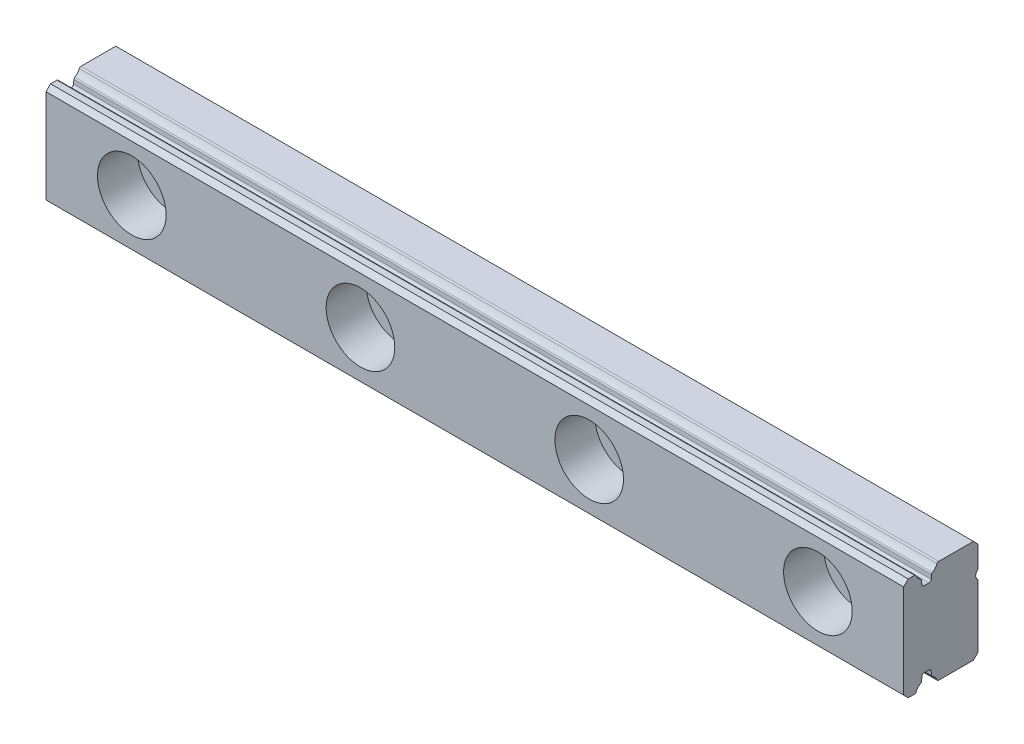
SolidWorks part; units mm, degrees
ref_plane "Front" through (0, 0, 0) normal (0, 0, 1) x (1, 0, 0)
ref_plane "Top" through (0, 0, 0) normal (0, 1, 0) x (1, 0, 0)
ref_plane "Right" through (0, 0, 0) normal (1, 0, 0) x (0, 0, -1)
ref_plane "Plane1" through (67.5, 0, 0) normal (1, 0, 0) x (0, 0, -1)
sketch "Sketch1" plane through (67.5, 0, 0) normal (1, 0, 0) x (0, 0, -1)
  line L0 (-3.4417, -4.5) -> (-0.4, -4.5)
  line L1 (-0.4, -4.5) -> (0, -4.1)
  line L2 (0, -4.1) -> (0, 1.4)
  line L3 (0, 2.2) -> (0, 4.1)
  line L4 (0, 4.1) -> (-0.4, 4.5)
  line L5 (-0.4, 4.5) -> (-3.4417, 4.5)
  line L6 (-4.0635, 3.8235) -> (-4.0934, 3.4826)
  line L7 (-4.2926, 3.3) -> (-4.7074, 3.3)
  line L8 (-4.9066, 3.4826) -> (-4.9365, 3.8235)
  line L9 (-5.5583, 4.5) -> (-6.1, 4.5)
  line L10 (-6.1, 4.5) -> (-6.5, 4.1)
  line L11 (-6.5, 4.1) -> (-6.5, -4.1)
  line L12 (-6.5, -4.1) -> (-6.1, -4.5)
  line L13 (-6.1, -4.5) -> (-5.5583, -4.5)
  line L14 (-4.9365, -3.8235) -> (-4.9066, -3.4826)
  line L15 (-4.7074, -3.3) -> (-4.2926, -3.3)
  line L16 (-4.0934, -3.4826) -> (-4.0635, -3.8235)
  arc A0 (0, 1.4) -> (0, 2.2) centre (0.3, 1.8) cw
  arc A1 (-3.4417, 4.5) -> (-3.5797, 4.4087) centre (-3.4417, 4.35) ccw
  arc A2 (-3.5797, 4.4087) -> (-3.9905, 3.9395) centre (-4.5, 4.8) cw
  arc A3 (-3.9905, 3.9395) -> (-4.0635, 3.8235) centre (-3.9141, 3.8104) ccw
  arc A4 (-4.0934, 3.4826) -> (-4.2926, 3.3) centre (-4.2926, 3.5) cw
  arc A5 (-4.7074, 3.3) -> (-4.9066, 3.4826) centre (-4.7074, 3.5) cw
  arc A6 (-4.9365, 3.8235) -> (-5.0095, 3.9395) centre (-5.0859, 3.8104) ccw
  arc A7 (-5.0095, 3.9395) -> (-5.4203, 4.4087) centre (-4.5, 4.8) cw
  arc A8 (-5.4203, 4.4087) -> (-5.5583, 4.5) centre (-5.5583, 4.35) ccw
  arc A9 (-5.5583, -4.5) -> (-5.4203, -4.4087) centre (-5.5583, -4.35) ccw
  arc A10 (-5.4203, -4.4087) -> (-5.0095, -3.9395) centre (-4.5, -4.8) cw
  arc A11 (-5.0095, -3.9395) -> (-4.9365, -3.8235) centre (-5.0859, -3.8104) ccw
  arc A12 (-4.9066, -3.4826) -> (-4.7074, -3.3) centre (-4.7074, -3.5) cw
  arc A13 (-4.2926, -3.3) -> (-4.0934, -3.4826) centre (-4.2926, -3.5) cw
  arc A14 (-4.0635, -3.8235) -> (-3.9905, -3.9395) centre (-3.9141, -3.8104) ccw
  arc A15 (-3.9905, -3.9395) -> (-3.5797, -4.4087) centre (-4.5, -4.8) cw
  arc A16 (-3.5797, -4.4087) -> (-3.4417, -4.5) centre (-3.4417, -4.35) ccw
extrude "Boss-Extrude1" add sketch "Sketch1" against normal blind 75
hole_wizard "CBORE for M3 Hex Head Machine Screw2" positions "Sketch5" profile "Sketch4" counterbore size "M3" standard "ANSI Metric"
sketch "Sketch5" plane through (0, 0, 6.5) normal (0, 0, 1) x (1, 0, 0)
  point P0 (0, 0)
sketch "Sketch4" plane through (0, 0, 6.5) normal (1, 0, 0) x (0, -1, 0)
  line L0 (0, 0) -> (0, 6.5)
  line L1 (0, 6.5) -> (1.75, 6.5)
  line L3 (1.75, 6.5) -> (1.75, 3.5)
  line L4 (1.75, 3.5) -> (3, 3.5)
  line L5 (3, 3.5) -> (3, 0)
  line L7 (3, 0) -> (0, 0)
  line L11 (0, -6.35) -> (0, 107.95) construction
  dimension "Thru Hole Dia." = 3.5
  dimension "Thru Hole Depth" = 6.5
  dimension "C'Bore Dia." = 6
  dimension "C'Bore Depth" = 3.5
pattern_linear "LPattern2" count 4 spacing 20 along (1, 0, 0) of "CBORE for M3 Hex Head Machine Screw2"
